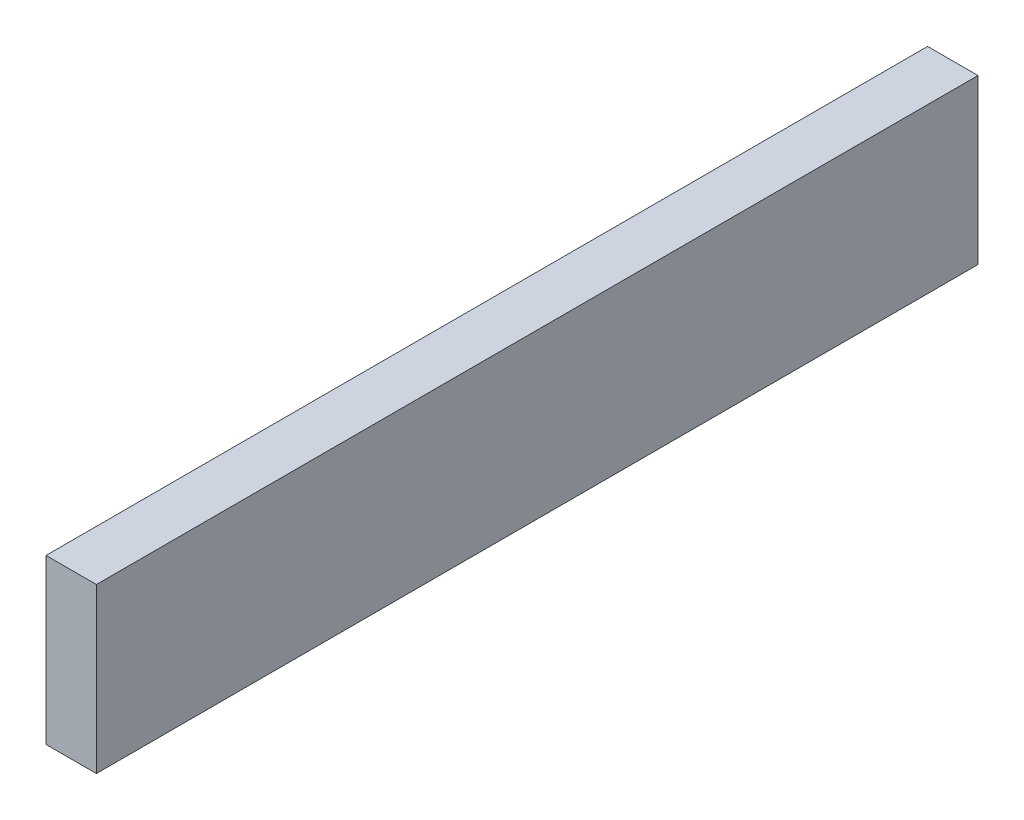
SolidWorks part; units mm, degrees
ref_plane "Front Plane" through (0, 0, 0) normal (0, 0, 1) x (1, 0, 0)
ref_plane "Top Plane" through (0, 0, 0) normal (0, 1, 0) x (1, 0, 0)
ref_plane "Right Plane" through (0, 0, 0) normal (1, 0, 0) x (0, 0, -1)
sketch "Sketch1" plane through (0, 0, 0) normal (0, 0, 1) x (1, 0, 0)
  line L1 (0, 0) -> (4, 0)
  line L2 (0, 0) -> (0, 13)
  line L3 (0, 13) -> (4, 13)
  line L4 (4, 0) -> (4, 13)
extrude "Boss-Extrude1" add sketch "Sketch1" along normal blind 70
